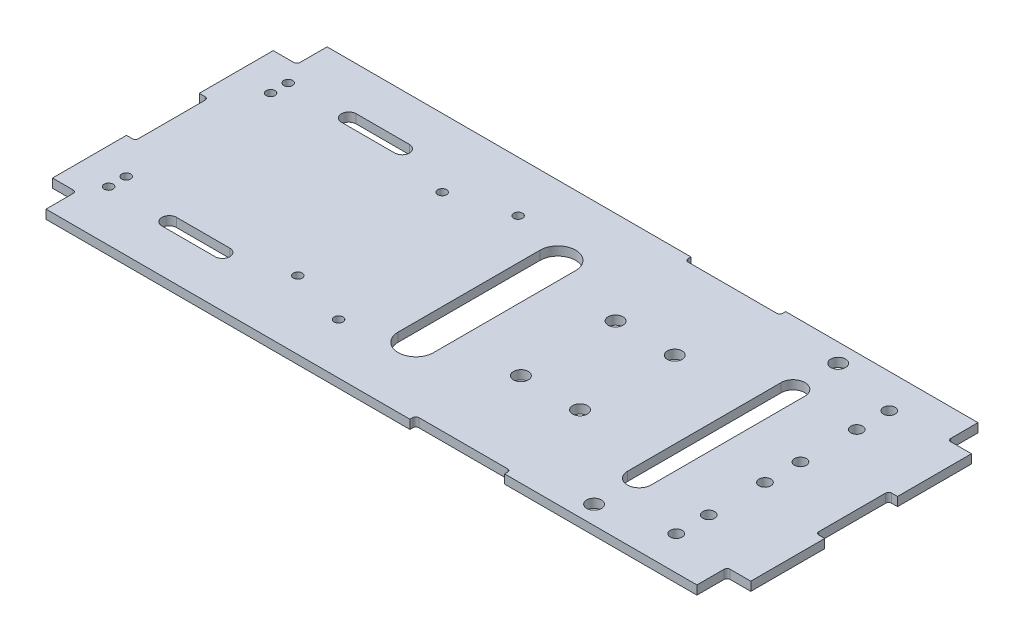
SolidWorks part; units mm, degrees
ref_plane "前视" through (0, 0, 0) normal (0, 0, 1) x (1, 0, 0)
ref_plane "上视" through (0, 0, 0) normal (0, 1, 0) x (1, 0, 0)
ref_plane "右视" through (0, 0, 0) normal (1, 0, 0) x (0, 0, -1)
sketch "草图4" plane through (0, 0, 0) normal (0, 1, 0) x (1, 0, 0)
  line L1 (-118, 47.5) -> (118, 47.5)
  line L2 (-118, 47.5) -> (-118, -47.5)
  line L3 (-118, -47.5) -> (118, -47.5)
  line L4 (118, 47.5) -> (118, -47.5)
  line L5 (-118, 47.5) -> (118, -47.5) construction
  line L6 (-118, -47.5) -> (118, 47.5) construction
  point P0 (0, 0)
  dimension "D1" = 236
  dimension "D2" = 95
extrude "凸台-拉伸3" add sketch "草图4" along normal blind 3
sketch "草图5" plane through (0, 3, 0) normal (0, 1, 0) x (1, 0, 0)
  line L0 (-123.3795, 0) -> (123.3795, 0) construction
  line L1 (-118, 0) -> (-115, 0)
  line L2 (-118, 47.5) -> (-118, -47.5) construction
  line L3 (-115, 0) -> (-115, 12.3)
  line L4 (-115, 12.3) -> (-118, 12.3)
  line L5 (-118, 12.3) -> (-118, 0)
  dimension "D1" = 3
  dimension "D2" = 12.3
extrude "切除-拉伸1" cut sketch "草图5" against normal through all
sketch "草图6" plane through (0, 3, 0) normal (0, 1, 0) x (1, 0, 0)
  line L0 (-131.3489, 37.3) -> (-63.4026, 37.3) construction
  line L1 (-115, 12.3) -> (-118, 12.3) construction
  line L2 (-118, 37.3) -> (-110, 37.3)
  line L3 (-118, 47.5) -> (-118, 12.3) construction
  line L4 (-110, 37.3) -> (-110, 47.5)
  line L5 (118, 47.5) -> (-118, 47.5) construction
  line L6 (-110, 47.5) -> (-118, 47.5)
  line L7 (-118, 47.5) -> (-118, 37.3)
  point P2 (-116.5, 12.3)
  dimension "D1" = 25
  dimension "D2" = 8
extrude "切除-拉伸2" cut sketch "草图6" against normal through all
fillet "圆角2" radius 1 1 edges at (-110, 1.5, -37.3)
fillet "圆角5" radius 1 1 edges at (-115, 1.5, -12.3)
sketch "草图7" plane through (0, 3, 0) normal (0, 1, 0) x (1, 0, 0)
  line L0 (-124.891, 0) -> (8.2781, 0) construction
  line L1 (-118, 0) -> (-115, 0)
  line L2 (-115, 0) -> (-115, -12.3)
  line L3 (-115, -12.3) -> (-118, -12.3)
  line L4 (-118, 0) -> (-118, -47.5) construction
  line L5 (-118, -12.3) -> (-118, 0)
  dimension "D1" = 12.3
extrude "切除-拉伸3" cut sketch "草图7" against normal through all
fillet "圆角6" radius 1 1 edges at (-115, 1.5, 12.3)
sketch "草图8" plane through (0, 3, 0) normal (0, 1, 0) x (1, 0, 0)
  line L0 (0, 0) -> (-144.9788, 0) construction
  line L1 (-144.9788, -37.3) -> (0, -37.3) construction
  line L2 (-118, -37.3) -> (-110, -37.3)
  line L3 (-110, -37.3) -> (-110, -47.5)
  line L4 (-118, -47.5) -> (118, -47.5) construction
  line L5 (-110, -47.5) -> (-118, -47.5)
  line L6 (-118, -37.3) -> (-118, -47.5)
  dimension "D1" = 37.3
  dimension "D2" = 8
extrude "切除-拉伸5" cut sketch "草图8" against normal through all
fillet "圆角9" radius 1 1 edges at (-110, 1.5, 37.3)
sketch "草图10" plane through (0, 3, 0) normal (0, 1, 0) x (1, 0, 0)
  line L0 (134.5344, 0) -> (0, 0) construction
  line L1 (118, 0) -> (115, 0)
  line L2 (115, 0) -> (115, 12.3)
  line L3 (115, 12.3) -> (118, 12.3)
  line L4 (118, -47.5) -> (118, 47.5) construction
  line L5 (118, 12.3) -> (118, 0)
  dimension "D1" = 12.3
  dimension "D2" = 3
extrude "切除-拉伸6" cut sketch "草图10" against normal through all
sketch "草图11" plane through (0, 3, 0) normal (0, 1, 0) x (1, 0, 0)
  line L0 (115.7031, 0) -> (0, 0) construction
  line L1 (118, 0) -> (115, 0)
  line L2 (115, 0) -> (115, -12.3)
  line L3 (115, -12.3) -> (118, -12.3)
  line L4 (118, -47.5) -> (118, 0) construction
  line L5 (118, -12.3) -> (118, 0)
  dimension "D1" = 12.3
extrude "切除-拉伸7" cut sketch "草图11" against normal through all
sketch "草图12" plane through (0, 3, 0) normal (0, 1, 0) x (1, 0, 0)
  line L0 (121.1687, 0) -> (0, 0) construction
  line L1 (138.0658, 37.3) -> (0, 37.3) construction
  line L2 (118, 37.3) -> (110, 37.3)
  line L3 (118, 12.3) -> (118, 47.5) construction
  line L4 (110, 37.3) -> (110, 47.5)
  line L5 (118, 47.5) -> (-110, 47.5) construction
  line L6 (110, 47.5) -> (118, 47.5)
  line L7 (118, 47.5) -> (118, 37.3)
  dimension "D1" = 37.3
  dimension "D2" = 8
extrude "切除-拉伸8" cut sketch "草图12" against normal through all
sketch "草图13" plane through (0, 3, 0) normal (0, 1, 0) x (1, 0, 0)
  line L0 (116.1404, 0) -> (0, 0) construction
  line L1 (0, -37.3) -> (128.8835, -37.3) construction
  line L2 (118, -47.5) -> (118, -37.3)
  line L3 (118, -47.5) -> (110, -47.5)
  line L4 (-110, -47.5) -> (118, -47.5) construction
  line L5 (110, -47.5) -> (110, -37.3)
  line L6 (118, -37.3) -> (110, -37.3)
  line L7 (118, -47.5) -> (118, -12.3) construction
  dimension "D1" = 37.3
  dimension "D2" = 8
extrude "切除-拉伸10" cut sketch "草图13" against normal through all
fillet "圆角13" radius 1 1 edges at (110, 1.5, -37.3)
fillet "圆角15" radius 1 1 edges at (110, 1.5, 37.3)
fillet "圆角18" radius 1 1 edges at (115, 1.5, 12.3)
fillet "圆角19" radius 1 1 edges at (115, 1.5, -12.3)
sketch "草图14" plane through (0, 3, 0) normal (0, 1, 0) x (1, 0, 0)
  line L0 (-120.6789, 0) -> (128.866, 0) construction
  line L1 (-85.5, 30.35) -> (-67.5, 30.35) construction
  line L2 (-8.5, 24) -> (-8.5, -24) construction
  line L3 (-2.5, 24) -> (-2.5, -24)
  line L4 (-14.5, 24) -> (-14.5, -24)
  line L5 (115, 11.3) -> (115, -11.3) construction
  line L6 (69, 26) -> (69, -26) construction
  line L7 (73, 26) -> (73, -26)
  line L8 (65, 26) -> (65, -26)
  line L9 (-85.5, 32.85) -> (-67.5, 32.85)
  line L10 (-118, 37.3) -> (-118, 12.3) construction
  line L11 (-85.5, 27.85) -> (-67.5, 27.85)
  line L13 (118, 12.3) -> (118, 37.3) construction
  line L28 (-85.5, -30.35) -> (-67.5, -30.35) construction
  line L29 (-85.5, -32.85) -> (-67.5, -32.85)
  line L30 (-85.5, -27.85) -> (-67.5, -27.85)
  line L47 (118, 12.3) -> (118, 37.3) construction
  circle A0 centre (-106, 30.35) radius 1.5
  circle A1 centre (-28.28, 30.35) radius 1.5
  circle A2 centre (-106, 24.4) radius 1.5
  circle A3 centre (-48, 24.4) radius 1.5
  arc A4 (-2.5, 24) -> (-14.5, 24) centre (-8.5, 24) ccw
  arc A5 (-14.5, -24) -> (-2.5, -24) centre (-8.5, -24) ccw
  circle A6 centre (91.5, 6) radius 2
  circle A7 centre (91.5, 25) radius 2
  circle A8 centre (91.5, 36) radius 2
  circle A9 centre (69, 41.25) radius 2.5
  circle A10 centre (39, 16) radius 2.5
  circle A11 centre (19, 16) radius 2.5
  arc A12 (73, 26) -> (65, 26) centre (69, 26) ccw
  arc A13 (65, -26) -> (73, -26) centre (69, -26) ccw
  arc A14 (-85.5, 32.85) -> (-85.5, 27.85) centre (-85.5, 30.35) ccw
  arc A15 (-67.5, 27.85) -> (-67.5, 32.85) centre (-67.5, 30.35) ccw
  circle A22 centre (91.5, -6) radius 2
  circle A23 centre (91.5, -25) radius 2
  circle A24 centre (91.5, -36) radius 2
  circle A25 centre (69, -41.25) radius 2.5
  circle A28 centre (39, -16) radius 2.5
  circle A29 centre (19, -16) radius 2.5
  circle A32 centre (-28.28, -30.35) radius 1.5
  circle A33 centre (-48, -24.4) radius 1.5
  arc A34 (-85.5, -32.85) -> (-85.5, -27.85) centre (-85.5, -30.35) cw
  arc A35 (-67.5, -27.85) -> (-67.5, -32.85) centre (-67.5, -30.35) cw
  circle A38 centre (-106, -24.4) radius 1.5
  circle A39 centre (-106, -30.35) radius 1.5
  point P15 (-8.5, 0)
  point P36 (69, 0)
  point P43 (-76.5, 30.35)
  point P85 (118, 24.8)
  point P103 (-76.5, -30.35)
  dimension "D1" = 30.35
  dimension "D3" = 3
  dimension "D4" = 30.35
  dimension "D6" = 3
  dimension "D8" = 58
  dimension "D13" = 6
  dimension "D15" = 25
  dimension "D16" = 36
  dimension "D17" = 46
  dimension "D19" = 16
  dimension "D21" = 50
  dimension "D25" = 3
  dimension "D26" = 3
  dimension "D27" = 30.35
  dimension "D30" = 5
  dimension "D31" = 5
  dimension "D5" = 77.72
  dimension "D7" = 24.4
  dimension "D9" = 97.5
  dimension "D10" = 12
  dimension "D11" = 12
  dimension "D12" = 48
  dimension "D14" = 23.5
  dimension "D18" = 41.25
  dimension "D20" = 30
  dimension "D22" = 8
  dimension "D23" = 52
  dimension "D24" = 12
  dimension "D28" = 5
  dimension "D29" = 41.5
  dimension "D32" = 18
  dimension "D37" = 26.5
  dimension "D38" = 26.5
extrude "切除-拉伸11" cut sketch "草图14" against normal through all
sketch "草图15" plane through (0, 3, 0) normal (0, 1, 0) x (1, 0, 0)
  line L0 (110, 47.5) -> (-110, 47.5) construction
  line L1 (13, 49.5) -> (45, 49.5)
  line L2 (13, 49.5) -> (13, 45.5)
  line L3 (13, 45.5) -> (45, 45.5)
  line L4 (45, 49.5) -> (45, 45.5)
  line L5 (13, 49.5) -> (45, 45.5) construction
  line L6 (13, 45.5) -> (45, 49.5) construction
  line L7 (110, 47.5) -> (110, 38.3) construction
  line L8 (0, 0) -> (3, 0) construction
  line L9 (13, -49.5) -> (13, -45.5)
  line L10 (13, -45.5) -> (45, -45.5)
  line L11 (45, -49.5) -> (45, -45.5)
  line L12 (13, -49.5) -> (45, -49.5)
  point P0 (29, 47.5)
  dimension "D1" = 4
  dimension "D2" = 81
  dimension "D3" = 32
extrude "切除-拉伸12" cut sketch "草图15" against normal through all
fillet "圆角20" radius 1 4 edges at (45, 1.5, 45.5) (13, 1.5, 45.5) (45, 1.5, -45.5) (13, 1.5, -45.5)
